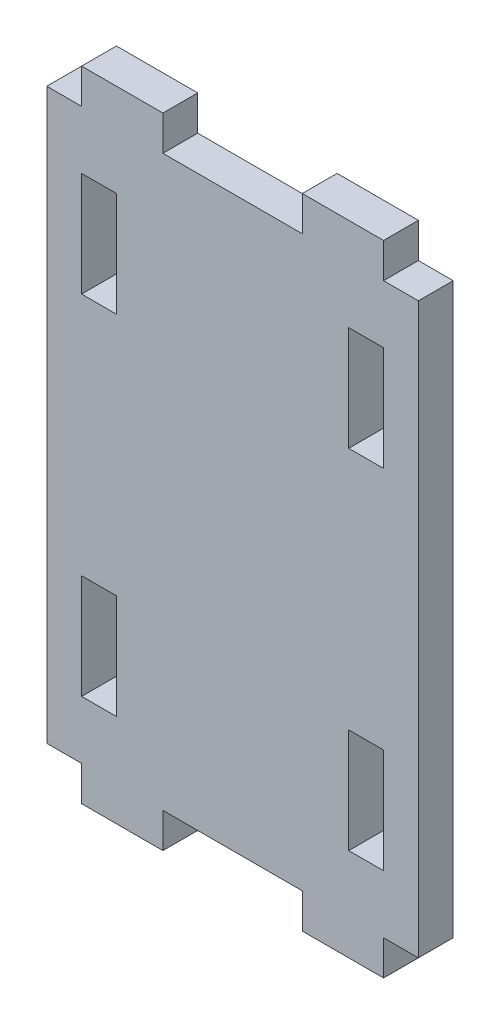
SolidWorks part; units mm, degrees
ref_plane "정면" through (0, 0, 0) normal (0, 0, 1) x (1, 0, 0)
ref_plane "윗면" through (0, 0, 0) normal (0, 1, 0) x (1, 0, 0)
ref_plane "우측면" through (0, 0, 0) normal (1, 0, 0) x (0, 0, -1)
sketch "스케치1" plane through (0, 0, 0) normal (0, 0, 1) x (1, 0, 0)
  line L1 (0, 0) -> (32, 0)
  line L2 (0, 0) -> (0, 55)
  line L3 (0, 55) -> (32, 55)
  line L4 (32, 0) -> (32, 55)
  dimension "D1" = 32
  dimension "D2" = 55
extrude "보스-돌출1" add sketch "스케치1" along normal blind 3
sketch "스케치2" plane through (0, 0, 3) normal (0, 0, 1) x (1, 0, 0)
  line L0 (0, 55) -> (0, 0) construction
  line L1 (0, 52) -> (3, 52)
  line L2 (0, 52) -> (0, 55)
  line L3 (0, 55) -> (32, 55)
  line L4 (32, 52) -> (32, 55)
  line L5 (10, 52) -> (22, 52)
  line L6 (3, 55) -> (10, 55)
  line L7 (3, 55) -> (3, 52)
  line L9 (10, 55) -> (10, 52)
  line L10 (22, 55) -> (29, 55)
  line L11 (22, 55) -> (22, 52)
  line L13 (29, 55) -> (29, 52)
  line L14 (29, 52) -> (32, 52)
  line L15 (-8.641, 27.5) -> (40.29, 27.5) construction
  line L16 (32, 3) -> (32, 0)
  line L17 (29, 3) -> (32, 3)
  line L18 (29, 0) -> (29, 3)
  line L19 (22, 0) -> (22, 3)
  line L20 (10, 3) -> (22, 3)
  line L21 (10, 0) -> (10, 3)
  line L22 (3, 0) -> (3, 3)
  line L23 (0, 3) -> (3, 3)
  line L24 (0, 3) -> (0, 0)
  line L25 (0, 0) -> (32, 0)
  point P15 (10, 53.5)
  line M12 (0, 55) -> (0, 0)
  line M13 (0, 0) -> (32, 0)
  line M14 (32, 0) -> (32, 55)
  line M15 (32, 55) -> (0, 55)
  dimension "D1" = 3
  dimension "D2" = 3
  dimension "D3" = 7
  dimension "D4" = 3
  dimension "D5" = 7
extrude "컷-돌출1" cut sketch "스케치2" against normal through all contours L7 L1 M15 M12 | L11 L9 L5 M15 | L13 L14 M14 M15 | L23 L22 M12 M13 | L21 L19 L20 M13 | L18 L17 M13 M14
sketch "스케치3" plane through (0, 0, 3) normal (0, 0, 1) x (1, 0, 0)
  line L0 (-4.7097, 27.5) -> (41.343, 27.5) construction
  line L1 (16, 54.7034) -> (16, 0) construction
  line L2 (0, 52) -> (3, 52) construction
  line L3 (3, 47) -> (6, 47)
  line L4 (3, 47) -> (3, 38)
  line L5 (3, 38) -> (6, 38)
  line L6 (6, 47) -> (6, 38)
  line L7 (29, 38) -> (26, 38)
  line L8 (26, 47) -> (26, 38)
  line L9 (29, 47) -> (26, 47)
  line L10 (29, 47) -> (29, 38)
  line L11 (29, 8) -> (29, 17)
  line L12 (29, 8) -> (26, 8)
  line L13 (26, 8) -> (26, 17)
  line L14 (29, 17) -> (26, 17)
  line L15 (3, 17) -> (6, 17)
  line L16 (6, 8) -> (6, 17)
  line L17 (3, 8) -> (6, 8)
  line L18 (3, 8) -> (3, 17)
  dimension "D1" = 3
  dimension "D2" = 9
  dimension "D3" = 5
extrude "컷-돌출2" cut sketch "스케치3" against normal through all
